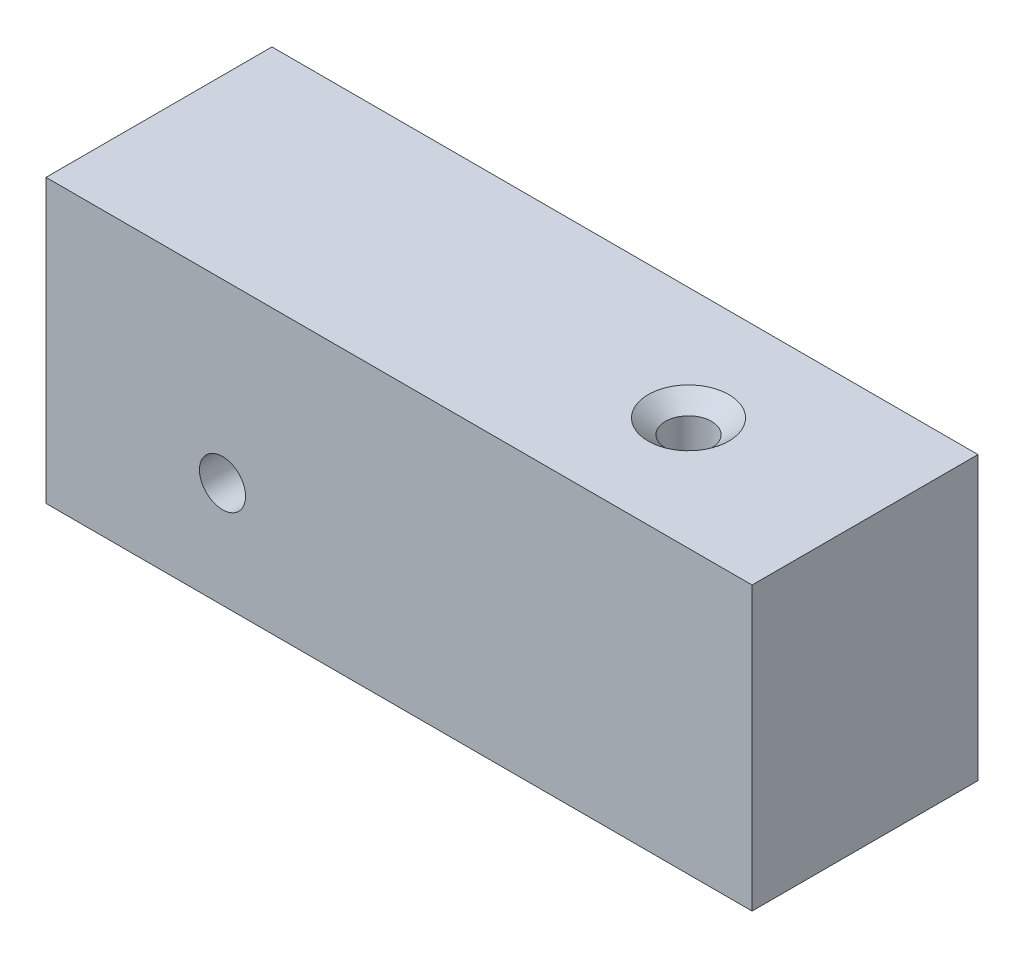
SolidWorks part; units mm, degrees
ref_plane "Front Plane" through (0, 0, 0) normal (0, 0, 1) x (1, 0, 0)
ref_plane "Top Plane" through (0, 0, 0) normal (0, 1, 0) x (1, 0, 0)
ref_plane "Right Plane" through (0, 0, 0) normal (1, 0, 0) x (0, 0, -1)
sketch "Sketch1" plane through (0, 0, 0) normal (0, 0, 1) x (1, 0, 0)
  line L1 (-25, 10) -> (25, 10)
  line L2 (-25, 10) -> (-25, -10)
  line L3 (-25, -10) -> (25, -10)
  line L4 (25, 10) -> (25, -10)
  point P4 (0, 10)
  point P5 (25, 0)
  dimension "D1" = 20
  dimension "D2" = 50
extrude "Boss-Extrude1" add sketch "Sketch1" against normal blind 16 contours L2 L3 L4 L1
hole_wizard "CSK for #4 Flat Head Machine Screw (100)1" positions "3DSketch1" profile "Sketch2" countersink size "#4" standard "ANSI Inch" end condition up to next
sketch3d "3DSketch1"
  line L2 (-25, 10, -16) -> (25, 10, -16) construction
  line L3 (-25, 10, -16) -> (-25, -10, -16) construction
  point P4 (-12.5, -2.5, -16)
  dimension "D1" = 12.5
  dimension "D2" = 12.5
sketch "Sketch2" plane through (-12.5, -2.5, -16) normal (1, 0, 0) x (0, 1, 0)
  line L0 (0, 0) -> (0, 16)
  line L1 (0, 16) -> (1.6319, 16)
  line L2 (1.6319, 16) -> (1.6319, 1.0284)
  line L3 (1.6319, 1.0284) -> (2.8575, 0)
  line L5 (2.8575, 0) -> (0, 0)
  line L6 (-1.6319, 1.0284) -> (-2.8575, 0) construction
  line L11 (0, -6.35) -> (0, 107.95) construction
  dimension "Thru Hole Dia." = 3.2639
  dimension "Thru Hole Depth" = 16
  dimension "Near C'Sink Dia." = 5.715
  dimension "Near C'Sink Angle" = 100
hole_wizard "CSK for #4 Flat Head Machine Screw (100)2" positions "Sketch3" profile "Sketch4" countersink size "#4" standard "ANSI Inch" end condition up to next
sketch "Sketch3" plane through (0, 10, 0) normal (0, 1, 0) x (1, 0, 0)
  line L1 (25, 16) -> (25, 0) construction
  line L2 (-25, 16) -> (25, 16) construction
  point P0 (12.5, 8)
  dimension "D2" = 12.5
  dimension "D3" = 8
sketch "Sketch4" plane through (12.5, 10, -8) normal (1, 0, 0) x (0, 0, 1)
  line L0 (0, 0) -> (0, 20)
  line L1 (0, 20) -> (1.6319, 20)
  line L2 (1.6319, 20) -> (1.6319, 1.0284)
  line L3 (1.6319, 1.0284) -> (2.8575, 0)
  line L5 (2.8575, 0) -> (0, 0)
  line L6 (-1.6319, 1.0284) -> (-2.8575, 0) construction
  line L11 (0, -6.35) -> (0, 107.95) construction
  dimension "Thru Hole Dia." = 3.2639
  dimension "Thru Hole Depth" = 20
  dimension "Near C'Sink Dia." = 5.715
  dimension "Near C'Sink Angle" = 100
